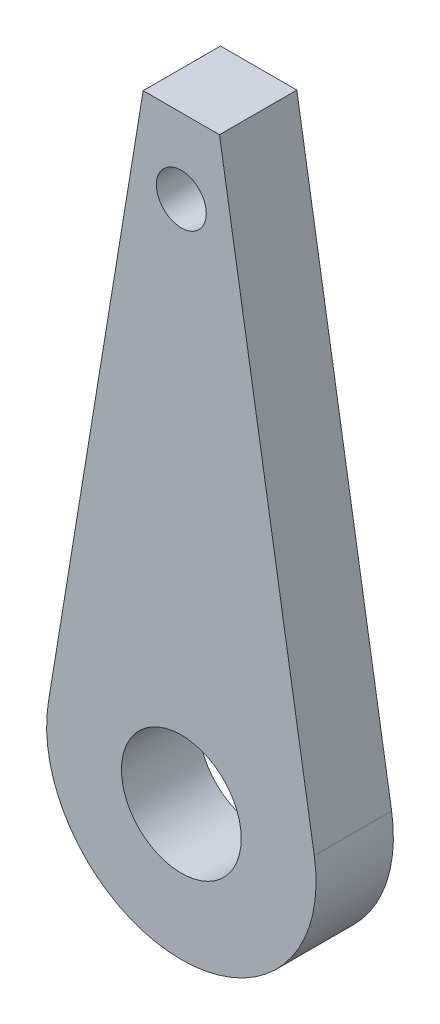
SolidWorks part; units mm, degrees
ref_plane "Front Plane" through (0, 0, 0) normal (0, 0, 1) x (1, 0, 0)
ref_plane "Top Plane" through (0, 0, 0) normal (0, 1, 0) x (1, 0, 0)
ref_plane "Right Plane" through (0, 0, 0) normal (1, 0, 0) x (0, 0, -1)
sketch "Sketch1" plane through (0, 0, 0) normal (0, 0, 1) x (1, 0, 0)
  line L0 (-19.0524, 36.6207) -> (-19.0524, 39.0207)
  line L4 (-20.582, 60.6207) -> (-17.5228, 60.6207)
  line L5 (-13.7238, 37.4961) -> (-17.5228, 60.6207)
  line L7 (-24.381, 37.4961) -> (-20.582, 60.6207)
  line L8 (-19.0524, 60.6207) -> (-19.0524, 57.6207)
  arc A2 (-24.381, 37.4961) -> (-13.7238, 37.4961) centre (-19.0524, 36.6207) ccw
  circle A5 centre (-19.0524, 36.6207) radius 2.4
  circle A6 centre (-19.0524, 57.6207) radius 1
extrude "Boss-Extrude1" add sketch "Sketch1" along normal blind 3.1
